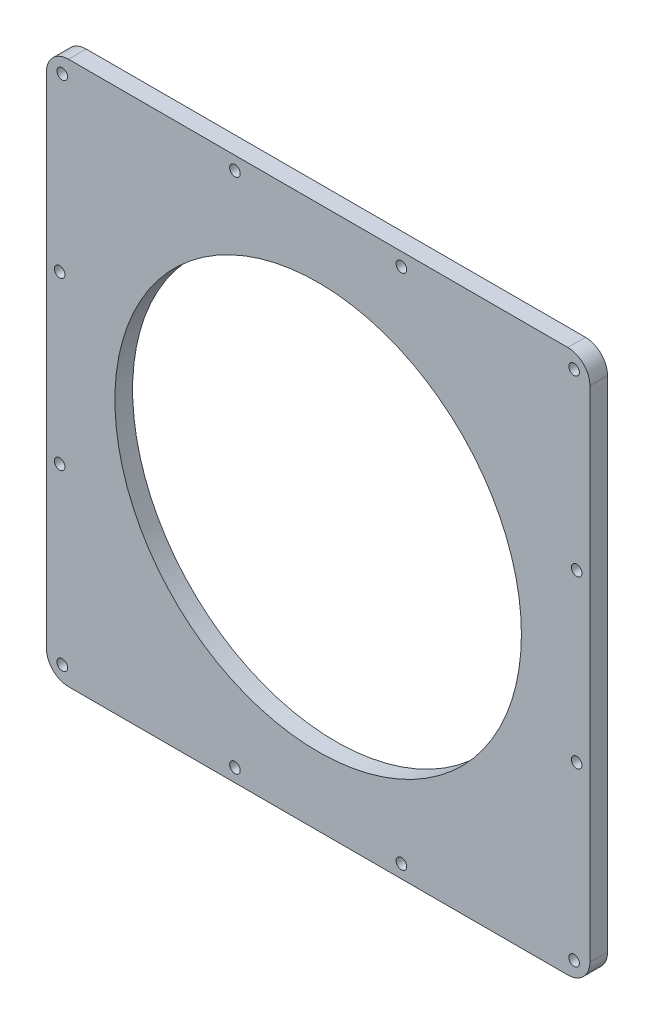
SolidWorks part; units mm, degrees
ref_plane "Front Plane" through (0, 0, 0) normal (0, 0, 1) x (1, 0, 0)
ref_plane "Top Plane" through (0, 0, 0) normal (0, 1, 0) x (1, 0, 0)
ref_plane "Right Plane" through (0, 0, 0) normal (1, 0, 0) x (0, 0, -1)
sketch "Sketch1" plane through (0, 0, 0) normal (0, 0, 1) x (1, 0, 0)
  line L1 (-61.5, -61.5) -> (61.5, -61.5)
  line L2 (-61.5, -61.5) -> (-61.5, 61.5)
  line L3 (-61.5, 61.5) -> (61.5, 61.5)
  line L4 (61.5, -61.5) -> (61.5, 61.5)
  line L5 (-61.5, -61.5) -> (61.5, 61.5) construction
  line L6 (-61.5, 61.5) -> (61.5, -61.5) construction
  circle A0 centre (0, 0) radius 14.5
  circle A1 centre (0, 0) radius 46
  circle A2 centre (0, 0) radius 34 construction
  dimension "D2" = 92
  dimension "D3" = 68
  dimension "D4" = 123
  dimension "D5" = 123
extrude "Boss-Extrude1" add sketch "Sketch1" along normal mid plane 4 contours L1 L4 L3 L2 A1
fillet "Fillet1" radius 5 4 edges at (61.5, -61.5, 0) (61.5, 61.5, 0) (-61.5, 61.5, 0) (-61.5, -61.5, 0)
hole_wizard "M2 Clearance Hole1" positions "Sketch5" profile "Sketch6" hole size "M2" standard "ANSI Metric" end condition up to next
sketch "Sketch5" plane through (0, 0, 2) normal (0, 0, 1) x (1, 0, 0)
  line L36 (58.5, 56.5) -> (58.5, -56.5) construction
  line L37 (56.5, -58.5) -> (-56.5, -58.5) construction
  line L38 (-58.5, -56.5) -> (-58.5, 56.5) construction
  line L39 (-56.5, 58.5) -> (56.5, 58.5) construction
  line L44 (61.5, -56.5) -> (61.5, 56.5) construction
  line L45 (-56.5, 61.5) -> (56.5, 61.5) construction
  line L46 (-56.5, -61.5) -> (56.5, -61.5) construction
  line L47 (-61.5, -56.5) -> (-61.5, 56.5) construction
  arc A25 (56.5, -58.5) -> (58.5, -56.5) centre (56.5, -56.5) ccw construction
  arc A26 (-58.5, -56.5) -> (-56.5, -58.5) centre (-56.5, -56.5) ccw construction
  arc A27 (-56.5, 58.5) -> (-58.5, 56.5) centre (-56.5, 56.5) ccw construction
  arc A32 (58.5, 56.5) -> (56.5, 58.5) centre (56.5, 56.5) ccw construction
  arc A37 (61.5, 56.5) -> (56.5, 61.5) centre (56.5, 56.5) ccw construction
  arc A38 (56.5, -61.5) -> (61.5, -56.5) centre (56.5, -56.5) ccw construction
  arc A39 (-61.5, -56.5) -> (-56.5, -61.5) centre (-56.5, -56.5) ccw construction
  arc A40 (-56.5, 61.5) -> (-61.5, 56.5) centre (-56.5, 56.5) ccw construction
  point P163 (-57.9142, 57.9142)
  point P176 (57.9142, 57.9142)
  point P178 (57.9142, -57.9142)
  point P180 (-57.9142, -57.9142)
  point P182 (-18.8333, -58.5)
  point P184 (18.8333, -58.5)
  point P186 (-58.5, -18.8333)
  point P188 (-58.5, 18.8333)
  point P190 (-18.8333, 58.5)
  point P192 (18.8333, 58.5)
  point P194 (58.5, 18.8333)
  point P196 (58.5, -18.8333)
  dimension "D7" = 3
  dimension "D8" = 3
  dimension "D9" = 2
  dimension "D11" = 2
  dimension "D12" = 3
  dimension "D14" = 2
  dimension "D15" = 3
  dimension "D16" = 2
  dimension "D1" = 3
  dimension "D2" = 3
  dimension "D3" = 37.6667
  dimension "D4" = 37.6667
  dimension "D5" = 37.6667
  dimension "D6" = 37.6667
  dimension "D10" = 3
  dimension "D13" = 3
sketch "Sketch6" plane through (58.5, -18.8333, 2) normal (1, 0, 0) x (0, -1, 0)
  line L0 (0, 0) -> (0, 4)
  line L1 (0, 4) -> (1.2, 4)
  line L2 (1.2, 4) -> (1.2, 0)
  line L5 (1.2, 0) -> (0, 0)
  line L11 (0, -6.35) -> (0, 107.95) construction
  dimension "Thru Hole Dia." = 2.4
  dimension "Thru Hole Depth" = 4
